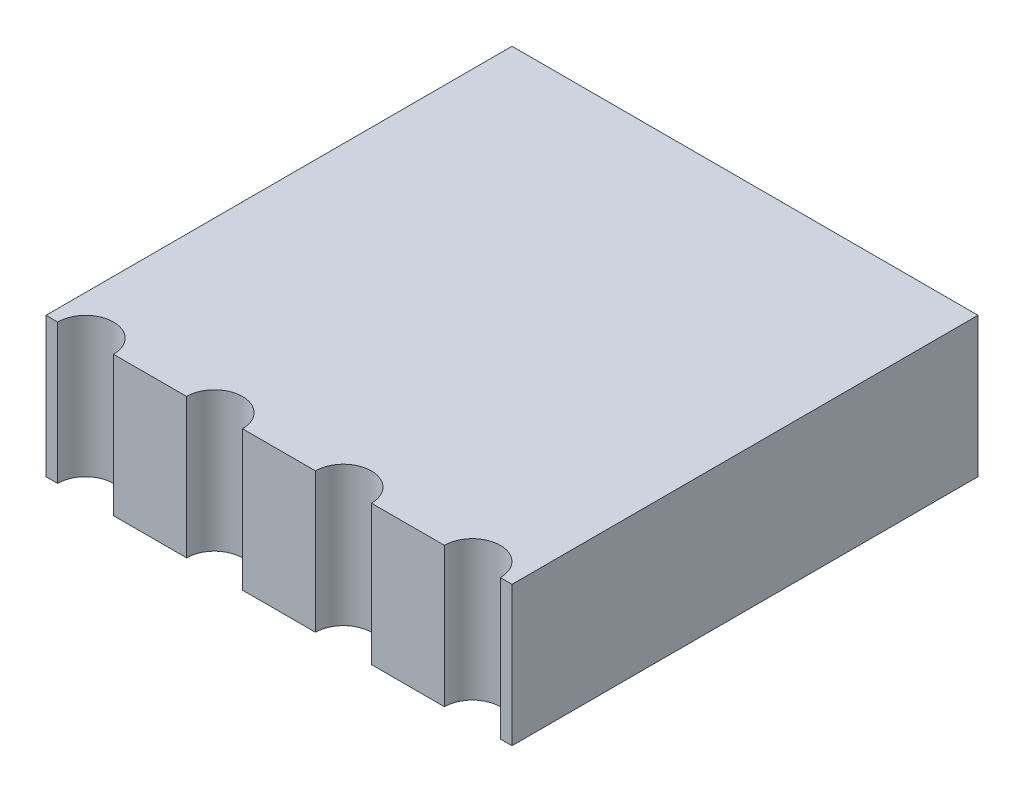
SolidWorks part; units mm, degrees
ref_plane "Front Plane" through (0, 0, 0) normal (0, 0, 1) x (1, 0, 0)
ref_plane "Top Plane" through (0, 0, 0) normal (0, 1, 0) x (1, 0, 0)
ref_plane "Right Plane" through (0, 0, 0) normal (1, 0, 0) x (0, 0, -1)
sketch "Sketch1" plane through (0, 0, 0) normal (0, 1, 0) x (1, 0, 0)
  line L0 (-5, 5) -> (5, -5) construction
  line L1 (-5, -5) -> (5, -5)
  line L2 (-5, -5) -> (-5, 5)
  line L3 (-5, 5) -> (5, 5)
  line L4 (5, -5) -> (5, 5)
  line L5 (-5, -5) -> (5, 5) construction
  point P4 (0, 0)
  dimension "D1" = 10
  dimension "D2" = 10
extrude "Boss-Extrude1" add sketch "Sketch1" along normal mid plane 3
sketch "Sketch2" plane through (0, 0, 0) normal (0, 1, 0) x (1, 0, 0)
  line L0 (-5, -5) -> (5, -5) construction
  line L1 (-4.75, -5) -> (-3.55, -5)
  line L2 (-5, 5) -> (-5, -5) construction
  arc A0 (-4.75, -5) -> (-3.55, -5) centre (-4.15, -5) cw
  dimension "D1" = 0.6
  dimension "D2" = 0.25
extrude "Cut-Extrude1" cut sketch "Sketch2" against normal mid plane 3
sketch "Sketch4" plane through (0, 1.5, 0) normal (0, 1, 0) x (1, 0, 0)
  line L0 (4.75, -5) -> (4.75, -1.7332) construction
  line L1 (-3.55, -5) -> (5, -5) construction
  line L2 (5, -5) -> (5, 5) construction
  dimension "D1" = 0.25
pattern_linear "LPattern1" count 4 spacing 2.7667 along (1, 0, 0) of "Cut-Extrude1"
sketch "Sketch5" plane through (0, -1.5, 0) normal (0, 1, 0) x (1, 0, 0)
  line L0 (0, -5) -> (0, 5)
  line L1 (-0.7833, -5) -> (0.7833, -5) construction
  line L2 (5, 5) -> (-5, 5) construction
sketch "Sketch6" plane through (0, 1.5, 0) normal (0, 1, 0) x (1, 0, 0)
  line L0 (0, -5) -> (0, 5)
  line L1 (-0.7833, -5) -> (0.7833, -5) construction
  line L2 (5, 5) -> (-5, 5) construction
